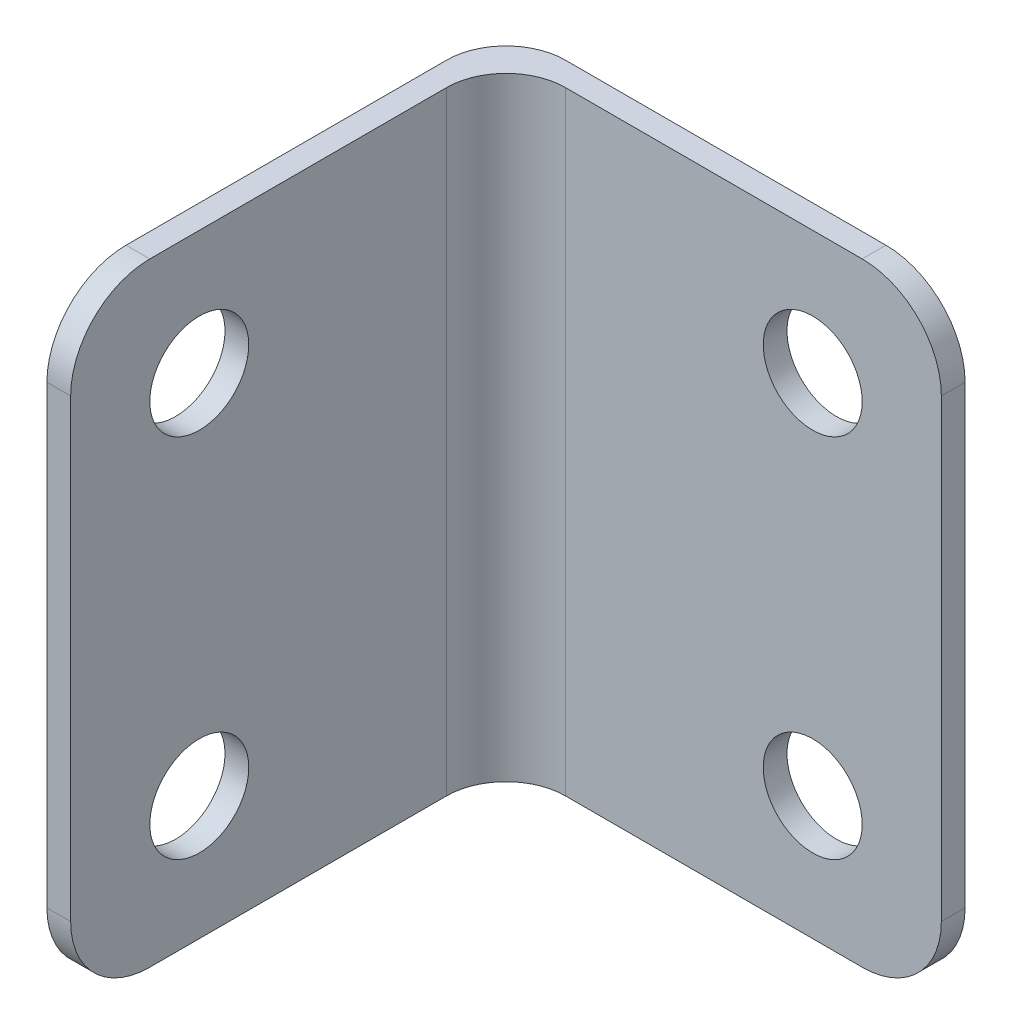
SolidWorks part; units mm, degrees
material "合金钢"
ref_plane "前视基准面" through (0, 0, 0) normal (0, 0, 1) x (1, 0, 0)
ref_plane "上视基准面" through (0, 0, 0) normal (0, 1, 0) x (1, 0, 0)
ref_plane "右视基准面" through (0, 0, 0) normal (1, 0, 0) x (0, 0, -1)
ref_plane "基准面4" through (0, 15.5, 0) normal (0, 1, 0) x (1, 0, 0)
sketch "草图1" plane through (0, 0, 0) normal (0, 1, 0) x (1, 0, 0)
  line L0 (3, 0) -> (23.2, 0)
  line L1 (0, -3) -> (0, -23.2)
  line L2 (23.2, 0) -> (23.2, -1.2)
  line L3 (23.2, -1.2) -> (4.2, -1.2)
  line L4 (1.2, -4.2) -> (1.2, -23.2)
  line L5 (1.2, -23.2) -> (0, -23.2)
  arc A2 (1.2, -4.2) -> (4.2, -1.2) centre (4.2, -4.2) cw
  arc A3 (0, -3) -> (3, 0) centre (3, -3) cw
  point P11 (0, 0)
  point P13 (0, 0)
  dimension "D5" = 3
  dimension "D6" = 3
  dimension "D1" = 23.2
  dimension "D2" = 23.2
  dimension "D3" = 1.2
  dimension "D4" = 1.2
extrude "凸台-拉伸1" add sketch "草图1" along normal blind 31
sketch "草图2" plane through (0, 0, 1.2) normal (0, 0, 1) x (1, 0, 0)
  line L0 (23.2, 31) -> (23.2, 0) construction
  line L1 (4.2, 31) -> (23.2, 31) construction
  line L2 (17.2, 31) -> (19.2, 31)
  line L3 (23.2, 27) -> (23.2, 25)
  line L4 (17.2, 31) -> (23.2, 31)
  line L5 (23.2, 31) -> (23.2, 25)
  line L8 (12.76, 15.5) -> (-12.76, 15.5) construction
  line L9 (23.2, 0) -> (23.2, 6)
  line L10 (17.2, 0) -> (23.2, 0)
  line L11 (23.2, 4) -> (23.2, 6)
  line L12 (17.2, 0) -> (19.2, 0)
  circle A0 centre (16.7, 24.75) radius 2.5
  arc A1 (23.2, 27) -> (19.2, 31) centre (19.2, 27) ccw
  arc A2 (23.2, 4) -> (19.2, 0) centre (19.2, 4) cw
  circle A3 centre (16.7, 6.25) radius 2.5
  point P13 (23.2, 31)
  line M7 (23.2, 0) -> (23.2, 31)
  line M8 (23.2, 31) -> (4.2, 31)
  dimension "D1" = 5
  dimension "D6" = 4
  dimension "D2" = 6.5
  dimension "D3" = 6.25
  dimension "D4" = 6
  dimension "D5" = 6
extrude "切除-拉伸1" cut sketch "草图2" against normal blind 30.5 contours A1 M7 M8 | A0 | A2 L10 M7 | A3
sketch "草图4" plane through (1.2, 0, 1) normal (1, 0, 0) x (0, 0, -1)
  line L0 (-22.2, 31) -> (-3.2, 31) construction
  line L18 (-22.2, 31) -> (-22.2, 0) construction
  line L21 (-16.2, 31) -> (-18.2, 31)
  line L22 (-22.2, 27) -> (-22.2, 25)
  line L23 (13.76, 15.5) -> (-11.76, 15.5) construction
  line L24 (-22.2, 4) -> (-22.2, 6)
  line L25 (-16.2, 0) -> (-18.2, 0)
  arc A9 (-18.2, 31) -> (-22.2, 27) centre (-18.2, 27) ccw
  circle A10 centre (-15.7, 6.25) radius 2.5
  circle A11 centre (-15.7, 24.75) radius 2.5
  arc A12 (-18.2, 0) -> (-22.2, 4) centre (-18.2, 4) cw
  point P9 (-22.2, 31)
  point P21 (-22.2, 0)
  line M20 (-22.2, 0) -> (-3.2, 0)
  line M22 (-3.2, 31) -> (-22.2, 31)
  line M23 (-22.2, 31) -> (-22.2, 0)
  dimension "D1" = 5
  dimension "D6" = 4
  dimension "D3" = 6.5
  dimension "D2" = 6.25
  dimension "D4" = 6
  dimension "D5" = 6
extrude "切除-拉伸2" cut sketch "草图4" against normal blind 30.5 contours A10 | A12 M20 M23 | A9 M22 M23 | A11
